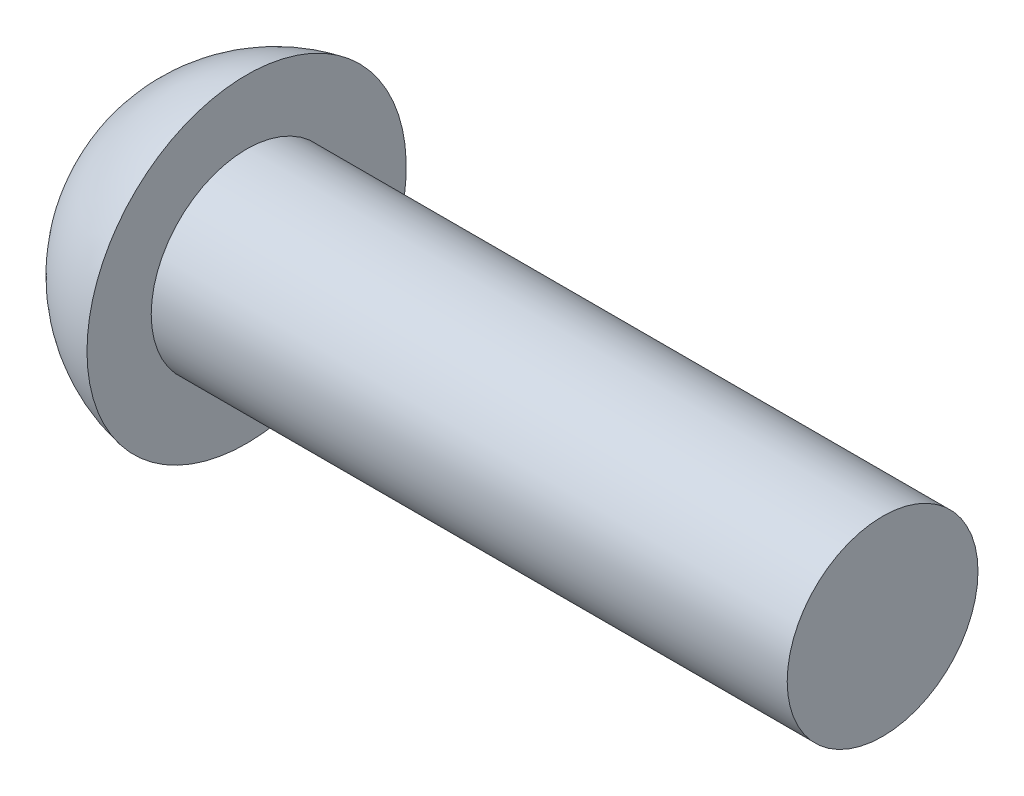
SolidWorks part; units mm, degrees
ref_plane "Plane1" through (0, 0, 0) normal (0, 0, 1) x (1, 0, 0)
ref_plane "Plane2" through (0, 0, 0) normal (0, 1, 0) x (1, 0, 0)
ref_plane "Plane3" through (0, 0, 0) normal (1, 0, 0) x (0, 0, -1)
sketch "BodySke" plane through (0, 0, 0) normal (0, 0, 1) x (1, 0, 0)
  line L0 (4.2, 3) -> (4.2, 5.02)
  line L1 (5.2, 15.875) -> (5.2, -8.7304) construction
  line L2 (-25.4, 0) -> (127, 0) construction
  line L3 (24.2, 0) -> (0, 0)
  line L4 (4.2, 3) -> (24.2, 3)
  line L5 (24.2, 3) -> (24.2, 0)
  line L8 (6.2, 0.7946) -> (6.2, -8.7304) construction
  arc A0 (4.2, 5.02) -> (0, 0) centre (5.1, 0) ccw
  dimension "Head_crown_rad" = 5.1
  dimension "Head_ht" = 4.2
  dimension "Diameter" = 6
  dimension "Length" = 20
  dimension "Head_dia" = 10.0399
  dimension "Advance" = 1
  dimension "Thread_nom" = 18
revolve "Base-Revolve" add sketch "BodySke" angle 360 about L2
cosmetic thread "ThreadCosmetic" parameters "Thread_length"=18, "Thread_minor"=4.891
sketch "Sketch3" plane through (0, 0, 0) normal (1, 0, 0) x (0, 0, -1)
  line L0 (0.41, -3.5) -> (-0.41, -3.5)
  line L1 (0.41, -3.5) -> (0.41, 3.5)
  line L2 (-0.41, 3.5) -> (0.41, 3.5)
  line L3 (-0.41, 3.5) -> (-0.41, -3.5)
  dimension "D1" = 3.5
  dimension "Cross_dia" = 7
  dimension "D2" = 0.41
  dimension "Cross_width" = 0.82
ref_plane "Plane4" through (3.2, 0, 0) normal (1, 0, 0) x (0, 0, -1)
sketch "Sketch4" plane through (3.2, 0, 0) normal (1, 0, 0) x (0, 0, -1)
  line L0 (0.41, -1.9045) -> (-0.41, -1.9045)
  line L1 (0.41, -1.9045) -> (0.41, 1.9045)
  line L2 (-0.41, 1.9045) -> (0.41, 1.9045)
  line L3 (-0.41, 1.9045) -> (-0.41, -1.9045)
  dimension "D1" = 0.82
  dimension "D2" = 3.8091
  dimension "D3" = 0.41
  dimension "D4" = 1.9045
loft "Recess" cut profiles "Sketch3", "Sketch4"
pattern_circular "RecPat" count 2 every 90 about axis through (0, 0, 0) along (1, 0, 0) of "Recess"
sketch "RecCorSke" plane through (0, 0, 0) normal (0, 0, 1) x (1, 0, 0)
  line L0 (-3.175, 0) -> (15.875, 0) construction
  line L1 (-25.4, 0) -> (127, 0) construction
  line L2 (0, 0) -> (0, 1.5043)
  line L3 (0, 1.5043) -> (3.2, 1.2805)
  line L4 (3.2, 1.2805) -> (3.6161, 0)
  line L5 (3.6161, 0) -> (0, 0)
  dimension "Diameter" = 2.561
  dimension "Depth" = 3.2
  dimension "Draft_angle" = 4
  dimension "Bottom_angle" = 18
revolve "RecessCore" cut sketch "RecCorSke" angle 360 about L0
sketch "Sketch5" plane through (0, 0, 0) normal (1, 0, 0) x (0, 0, -1)
  line L0 (-0.9, -4.9386) -> (-0.9, 4.9386)
  line L1 (0, 5.02) -> (0, -5.02) construction
  line L2 (0.9, -4.9386) -> (0.9, 4.9386)
  circle A0 centre (0, 0) radius 5.02 construction
  arc A1 (0.9, 4.9386) -> (-0.9, 4.9386) centre (0, 0) ccw
  arc A2 (-0.9, -4.9386) -> (0.9, -4.9386) centre (0, 0) ccw
  dimension "Slot_width" = 1.8
extrude "Slot" [suppressed] cut sketch "Sketch5" along normal blind 2.5
equation "\"D1@Sketch3\" = \"Cross_dia@Sketch3\" / 2"
equation "\"D2@Sketch3\" = \"Cross_width@Sketch3\" / 2"
equation "\"Depth@RecCorSke\" = \"Cross_depth@Plane4\""
equation "\"D1@Sketch4\" = \"Cross_width@Sketch3\""
equation "\"D2@Sketch4\" = \"Cross_dia@Sketch3\" - 2.0 * \"Cross_depth@Plane4\" * tan(26.5  * 0.017453292)"
equation "\"D3@Sketch4\" = \"D1@Sketch4\" / 2"
equation "\"D4@Sketch4\" = \"D2@Sketch4\" / 2"
equation "\"Thread_length@ThreadCosmetic\" = ((sgn( (\"Length@BodySke\" - \"Advance@BodySke\" * 2.0 ) - \"Thread_nom@BodySke\" )-1)*( (\"Length@BodySke\" - \"Advance@BodySke\" * 2.0 ) - \"Thread_nom@BodySke\" ))/-2+ \"Thread_nom@BodySke\""
